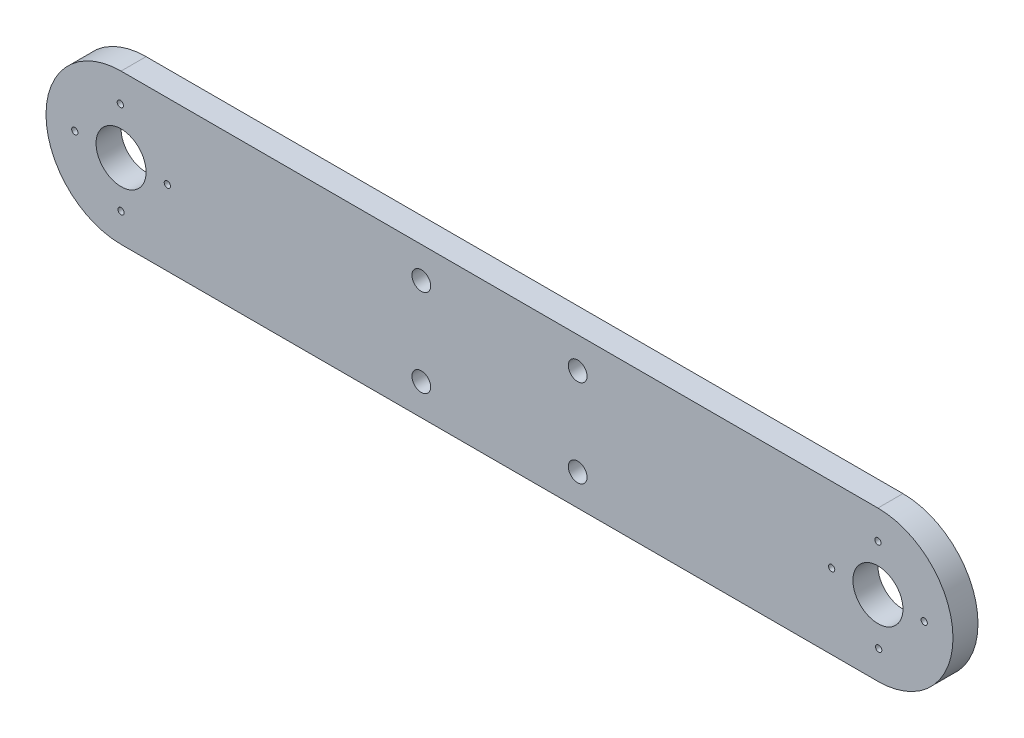
SolidWorks part; units mm, degrees
material "Beech"
ref_plane "Front Plane" through (0, 0, 0) normal (0, 0, 1) x (1, 0, 0)
ref_plane "Top Plane" through (0, 0, 0) normal (0, 1, 0) x (1, 0, 0)
ref_plane "Right Plane" through (0, 0, 0) normal (1, 0, 0) x (0, 0, -1)
sketch "Sketch1" plane through (0, 0, 0) normal (0, 0, 1) x (1, 0, 0)
  line L0 (12, 24) -> (133, 24)
  line L1 (133, 0) -> (12, 0)
  arc A0 (12, 24) -> (12, 0) centre (12, 12) ccw
  arc A1 (133, 0) -> (133, 24) centre (133, 12) ccw
  circle A2 centre (133, 12) radius 4
  circle A3 centre (133, 19.4) radius 0.5
  circle A4 centre (133.121, 4.601) radius 0.5
  circle A5 centre (140.4, 12) radius 0.5
  circle A6 centre (125.6, 12) radius 0.5
  circle A7 centre (60, 5) radius 1.5
  circle A8 centre (60, 19) radius 1.5
  circle A9 centre (85, 5) radius 1.5
  circle A10 centre (85, 19) radius 1.5
  circle A11 centre (12, 12) radius 4
  circle A12 centre (12, 4.6) radius 0.5
  circle A13 centre (11.879, 19.399) radius 0.5
  circle A14 centre (4.6, 12) radius 0.5
  circle A15 centre (19.4, 12) radius 0.5
extrude "Boss-Extrude1" add sketch "Sketch1" along normal blind 4
